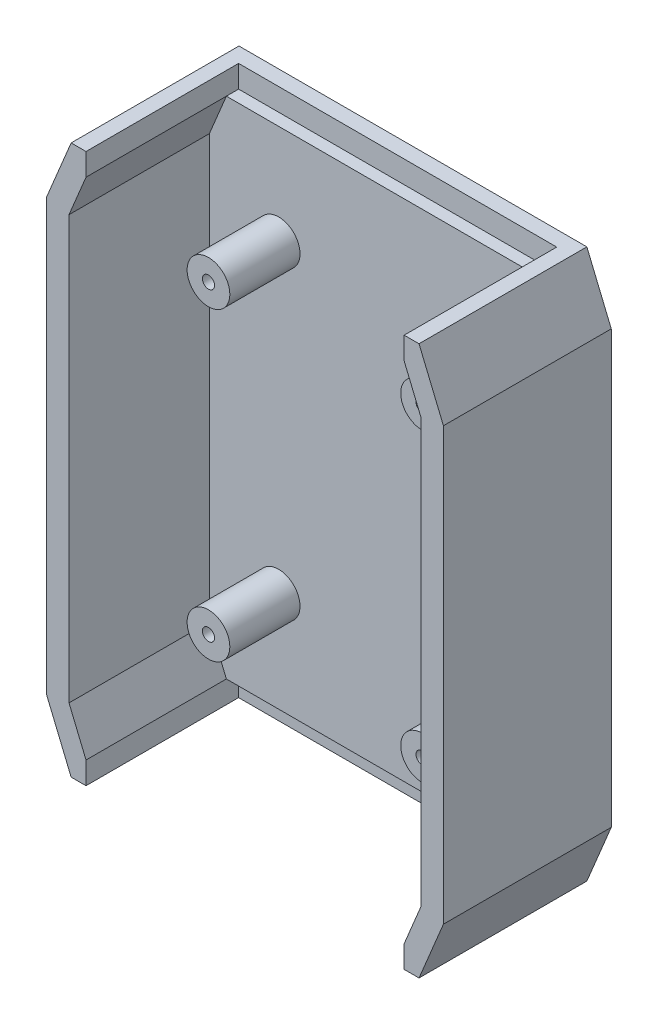
SolidWorks part; units mm, degrees
ref_plane "Front Plane" through (0, 0, 0) normal (0, 0, 1) x (1, 0, 0)
ref_plane "Top Plane" through (0, 0, 0) normal (0, 1, 0) x (1, 0, 0)
ref_plane "Right Plane" through (0, 0, 0) normal (1, 0, 0) x (0, 0, -1)
sketch "Sketch1" plane through (0, 0, 0) normal (0, 0, 1) x (1, 0, 0)
  line L0 (36.195, 57.15) -> (41.275, 44.9144)
  line L1 (-41.275, 57.15) -> (41.275, 57.15)
  line L2 (-41.275, 57.15) -> (-41.275, -57.15)
  line L3 (-41.275, -57.15) -> (41.275, -57.15)
  line L4 (41.275, 57.15) -> (41.275, -57.15)
  line L5 (-41.275, 57.15) -> (41.275, -57.15) construction
  line L6 (-41.275, -57.15) -> (41.275, 57.15) construction
  line L7 (0, 33.4719) -> (0, -22.1917) construction
  line L8 (-26.0475, 0) -> (21.028, 0) construction
  line L9 (-36.195, 57.15) -> (-41.275, 44.9144)
  line L10 (36.195, -57.15) -> (41.275, -44.9144)
  line L11 (-36.195, -57.15) -> (-41.275, -44.9144)
  point P0 (0, 0)
  dimension "D1" = 82.55
  dimension "D2" = 114.3
  dimension "D3" = 5.08
extrude "Boss-Extrude1" add sketch "Sketch1" along normal blind 5.715 contours L11 L3 L10 L4 L0 L1 L9 L2
sketch "Sketch2" plane through (0, 0, 5.715) normal (0, 0, 1) x (1, 0, 0)
  line L0 (-36.2798, 57.277) -> (-41.402, 44.9397)
  line L1 (-41.402, 44.9397) -> (-41.402, -44.9397)
  line L2 (-41.402, -44.9397) -> (-36.2798, -57.277)
  line L3 (-36.2798, -57.277) -> (36.2798, -57.277)
  line L4 (36.2798, -57.277) -> (41.402, -44.9397)
  line L5 (41.402, -44.9397) -> (41.402, 44.9397)
  line L6 (41.402, 44.9397) -> (36.2798, 57.277)
  line L7 (36.2798, 57.277) -> (-36.2798, 57.277)
  line L42 (41.275, 44.9144) -> (36.195, 57.15)
  line L43 (36.195, 57.15) -> (-36.195, 57.15)
  line L44 (-36.195, 57.15) -> (-41.275, 44.9144)
  line L45 (-41.275, 44.9144) -> (-41.275, -44.9144)
  line L46 (-41.275, -44.9144) -> (-36.195, -57.15)
  line L47 (-36.195, -57.15) -> (36.195, -57.15)
  line L48 (36.195, -57.15) -> (41.275, -44.9144)
  line L49 (41.275, -44.9144) -> (41.275, 44.9144)
  line L50 (36.6395, 43.9904) -> (33.1004, 52.5145)
  line L51 (36.6395, -43.9904) -> (36.6395, 43.9904)
  line L52 (33.1004, 52.5145) -> (-33.1004, 52.5145)
  line L53 (33.1004, -52.5145) -> (36.6395, -43.9904)
  line L54 (-33.1004, -52.5145) -> (33.1004, -52.5145)
  line L55 (-36.6395, -43.9904) -> (-33.1004, -52.5145)
  line L56 (-36.6395, 43.9904) -> (-36.6395, -43.9904)
  line L57 (-33.1004, 52.5145) -> (-36.6395, 43.9904)
  line L58 (36.6395, 43.9904) -> (33.1004, 52.5145)
  line L59 (36.6395, -43.9904) -> (36.6395, 43.9904)
  line L60 (33.1004, 52.5145) -> (-33.1004, 52.5145)
  line L61 (33.1004, -52.5145) -> (36.6395, -43.9904)
  line L62 (-33.1004, -52.5145) -> (33.1004, -52.5145)
  line L63 (-36.6395, -43.9904) -> (-33.1004, -52.5145)
  line L64 (-36.6395, 43.9904) -> (-36.6395, -43.9904)
  line L65 (-33.1004, 52.5145) -> (-36.6395, 43.9904)
  line M9 (-41.275, -44.9144) -> (-36.195, -57.15)
  line M10 (-36.195, -57.15) -> (36.195, -57.15)
  line M11 (36.195, -57.15) -> (41.275, -44.9144)
  line M12 (41.275, -44.9144) -> (41.275, 44.9144)
  line M13 (41.275, 44.9144) -> (36.195, 57.15)
  line M14 (36.195, 57.15) -> (-36.195, 57.15)
  line M15 (-36.195, 57.15) -> (-41.275, 44.9144)
  line M16 (-41.275, 44.9144) -> (-41.275, -44.9144)
  dimension "D1" = 4.6355
  dimension "D2" = 4.6355
  dimension "D3" = 4.7625
extrude "Boss-Extrude2" add sketch "Sketch2" along normal blind 29.21 contours L65 L60 L58 L59 L61 L62 L63 L64 M16 M9 M10 M11 M12 M13 M14 M15
sketch "Sketch3" plane through (0, 0, 34.925) normal (0, 0, 1) x (1, 0, 0)
  line L0 (36.195, 57.15) -> (-36.195, 57.15) construction
  line L1 (-33.1004, 52.5145) -> (33.1004, 52.5145)
  line L2 (-33.1004, 52.5145) -> (-33.1004, 57.15)
  line L3 (-33.1004, 57.15) -> (33.1004, 57.15)
  line L4 (33.1004, 52.5145) -> (33.1004, 57.15)
extrude "Cut-Extrude1" cut sketch "Sketch3" against normal blind 31.75
mirror "Mirror1" about plane through (0, 0, 0) normal (0, 1, 0) of "Cut-Extrude1"
sketch "Sketch4" plane through (0, 0, 5.715) normal (0, 0, 1) x (1, 0, 0)
  line L0 (33.1004, 57.15) -> (-33.1004, 57.15) construction
  line L1 (-41.275, 44.9144) -> (-41.275, -44.9144) construction
  line L2 (33.1004, -57.15) -> (-33.1004, -57.15) construction
  circle A0 centre (22.225, -31.75) radius 4.445
  circle A1 centre (-22.225, -31.75) radius 4.445
  circle A2 centre (22.225, 31.75) radius 4.445
  circle A3 centre (-22.225, 31.75) radius 4.445
  point P10 (0, 0)
  dimension "D1" = 8.89
  dimension "D2" = 8.89
  dimension "D3" = 8.89
  dimension "D4" = 8.89
  dimension "D5" = 25.4
  dimension "D6" = 25.4
  dimension "D7" = 44.45
  dimension "D8" = 19.05
  dimension "D9" = 0
  dimension "D10" = 25.4
  dimension "D11" = 25.4
  dimension "D12" = 44.45
extrude "Boss-Extrude3" add sketch "Sketch4" along normal blind 14.605
sketch "Sketch5" plane through (0, 0, 20.32) normal (0, 0, 1) x (1, 0, 0)
  circle A0 centre (-22.225, 31.75) radius 1.27
  circle A1 centre (22.225, 31.75) radius 1.27
  circle A2 centre (22.225, -31.75) radius 1.27
  circle A3 centre (-22.225, -31.75) radius 1.27
  dimension "D1" = 2.54
  dimension "D2" = 2.54
  dimension "D3" = 2.54
  dimension "D4" = 2.54
extrude "Cut-Extrude2" cut sketch "Sketch5" against normal blind 7.62
